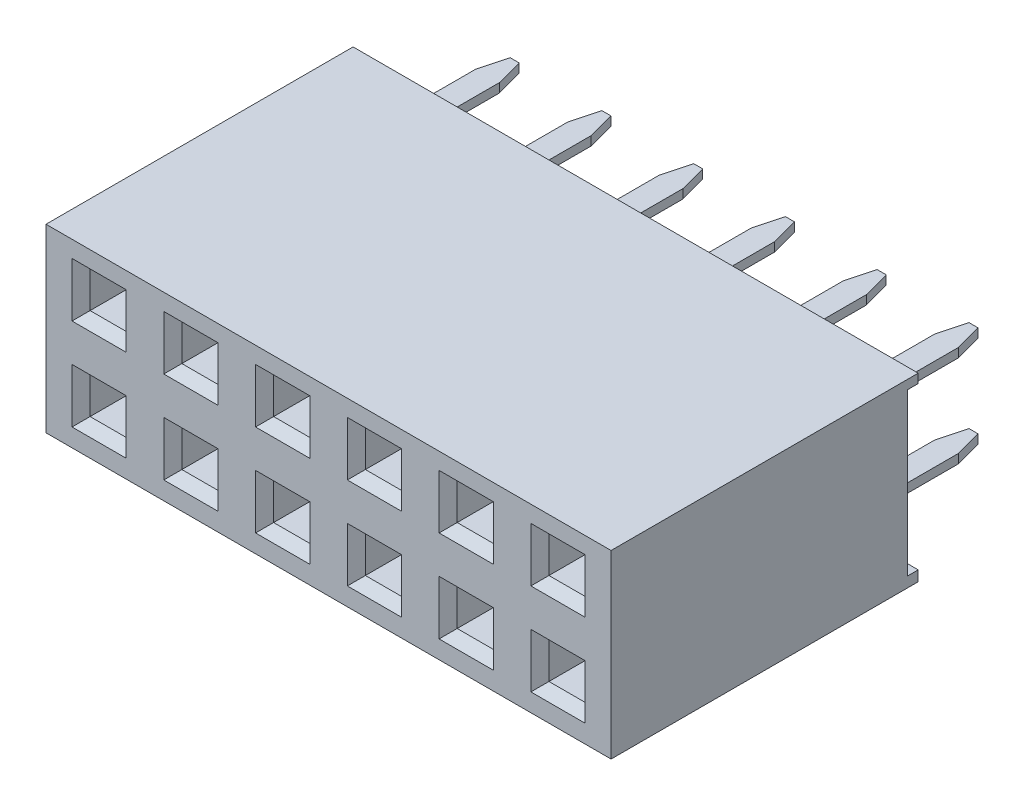
SolidWorks part; units mm, degrees
ref_plane "Front Plane" through (0, 0, 0) normal (0, 0, 1) x (1, 0, 0)
ref_plane "Top Plane" through (0, 0, 0) normal (0, 1, 0) x (1, 0, 0)
ref_plane "Right Plane" through (0, 0, 0) normal (1, 0, 0) x (0, 0, -1)
sketch "Sketch1" plane through (0, 0, 0) normal (0, 0, 1) x (1, 0, 0)
  line L1 (0, 0) -> (15.64, 0)
  line L2 (0, 0) -> (0, 5)
  line L3 (0, 5) -> (15.64, 5)
  line L4 (15.64, 0) -> (15.64, 5)
  dimension "width" = 5
  dimension "length" = 15.64
extrude "Boss-Extrude1" add sketch "Sketch1" along normal blind 8.5
sketch "Sketch2" plane through (0, 0, 8.5) normal (0, 0, 1) x (1, 0, 0)
  line L0 (0, 1.25) -> (15.64, 1.25) construction
  line L1 (0, 5) -> (0, 0) construction
  line L2 (15.64, 0) -> (15.64, 5) construction
  line L3 (0, 0) -> (15.64, 0) construction
  line L5 (15.64, 5) -> (0, 5) construction
  line L6 (1.47, 5) -> (1.47, 0) construction
  line L7 (0.97, 1.75) -> (1.97, 1.75)
  line L8 (0.97, 1.75) -> (0.97, 0.75)
  line L9 (0.97, 0.75) -> (1.97, 0.75)
  line L10 (1.97, 1.75) -> (1.97, 0.75)
  point P16 (1.47, 1.75)
  point P17 (1.97, 1.25)
  dimension "D1" = 1.25
  dimension "D2" = 1.47
  dimension "D3" = 1
  dimension "D4" = 1
extrude "Cut-Extrude1" cut sketch "Sketch2" against normal blind 2.25
chamfer "Chamfer1" distance 0.25 angle 45 4 edges at (0.97, 1.25, 8.5) (1.47, 0.75, 8.5) (1.97, 1.25, 8.5) (1.47, 1.75, 8.5)
sketch "Sketch3" plane through (0, 0, 0) normal (-1, 0, 0) x (0, 0, 1)
  line L0 (0, 5) -> (0, 0) construction
  line L1 (0, 4.75) -> (0.3, 4.75)
  line L2 (0, 4.75) -> (0, 0.2861)
  line L3 (0, 0.2861) -> (0.3, 0.2861)
  line L4 (0.3, 4.75) -> (0.3, 0.2861)
  line L5 (8.5, 2.5) -> (0, 2.5181) construction
  line L6 (8.5, 5) -> (0, 5) construction
  line L7 (8.5, 5) -> (8.5, 0) construction
  dimension "D1" = 0.25
  dimension "D2" = 0.3
extrude "Cut-Extrude2" cut sketch "Sketch3" against normal through all
ref_plane "Plane1" through (0, 1.25, 0) normal (0, -1, 0) x (-1, 0, 0)
sketch "Sketch4" plane through (0, 1.25, 0) normal (0, -1, 0) x (-1, 0, 0)
  line L0 (-1.47, -8.25) -> (-1.47, -0.3) construction
  line L1 (-0.97, -8.25) -> (-1.97, -8.25) construction
  line L2 (-15.64, -0.3) -> (0, -0.3) construction
  line L3 (0, 0) -> (-15.64, 0) construction
  line L4 (-1.795, -0.3) -> (-1.145, -0.3)
  line L5 (-1.795, -0.3) -> (-1.795, 3)
  line L6 (-1.795, 3) -> (-1.145, 3)
  line L7 (-1.145, -0.3) -> (-1.145, 3)
  point P10 (-1.47, -0.3)
  dimension "D1" = 0.65
  dimension "D2" = 3
extrude "Boss-Extrude2" add sketch "Sketch4" along normal mid plane 0.25 separate body
chamfer "Chamfer2" distance 0.2 angle 75 2 edges at (1.145, 1.25, -3) (1.795, 1.25, -3)
pattern_linear "LPattern4" count 6 spacing 2.54 along (1, 0, 0) count 2 spacing 2.54 along (0, 1, 0) of bodies 104
pattern_linear "LPattern5" count 6 spacing 2.54 along (1, 0, 0) count 2 spacing 2.54 along (0, 1, 0) of "Cut-Extrude1", "Chamfer1"
equation "\"pins\" = 6"
equation "\"rows\" = 2"
equation "\"length\"= 2.54 * \"pins\" + .4"
equation "\"width\"= 2.5 * \"rows\""
equation "\"width@Sketch1\"= 2.5 * \"rows\""
equation "\"length@Sketch1\"= 2.54 * \"pins\" + .4"
equation "\"D2@LPattern5\"= \"rows\""
equation "\"D2@LPattern4\"= \"rows\""
equation "\"D1@LPattern4\"= \"pins\""
equation "\"D1@LPattern5\"= \"pins\""
